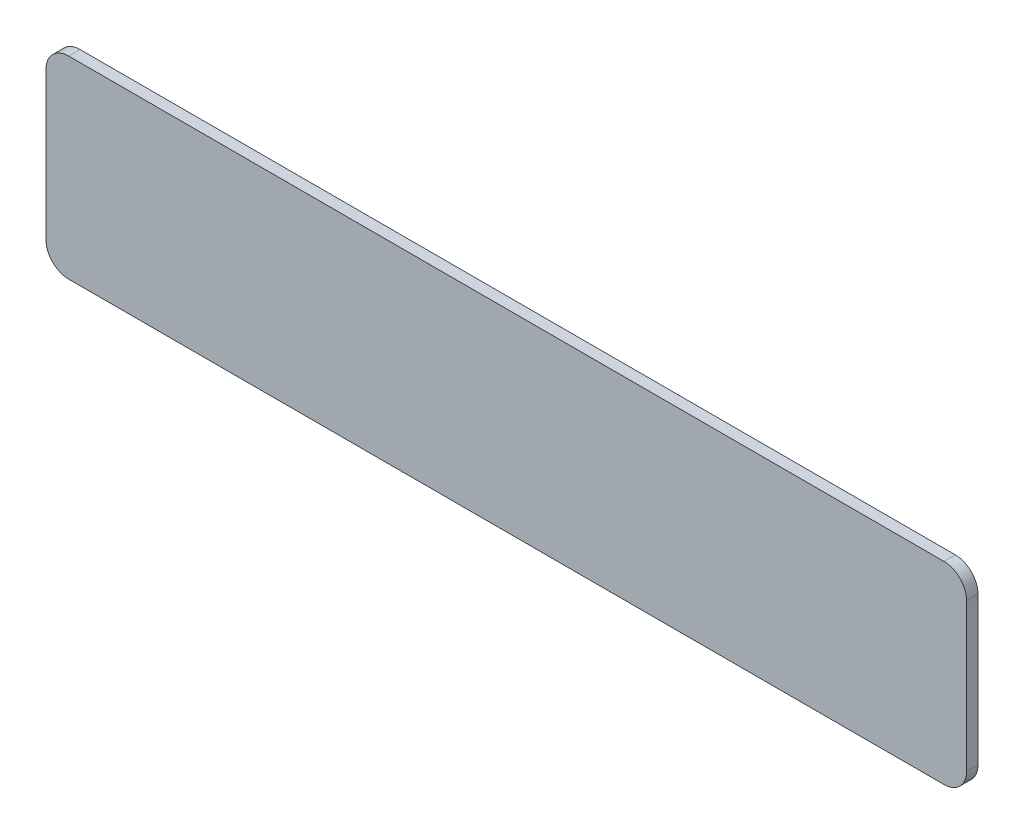
SolidWorks part; units mm, degrees
ref_plane "Front Plane" through (0, 0, 0) normal (0, 0, 1) x (1, 0, 0)
ref_plane "Top Plane" through (0, 0, 0) normal (0, 1, 0) x (1, 0, 0)
ref_plane "Right Plane" through (0, 0, 0) normal (1, 0, 0) x (0, 0, -1)
sketch "Sketch1" plane through (0, 0, 0) normal (0, 0, 1) x (1, 0, 0)
  line L1 (-38.5, 8.5) -> (38.5, 8.5)
  line L2 (-40.5, 6.5) -> (-40.5, -6.5)
  line L3 (-38.5, -8.5) -> (38.5, -8.5)
  line L4 (40.5, 6.5) -> (40.5, -6.5)
  line L5 (-40.5, 8.5) -> (40.5, -8.5) construction
  line L6 (-40.5, -8.5) -> (40.5, 8.5) construction
  arc A0 (38.5, 8.5) -> (40.5, 6.5) centre (38.5, 6.5) cw
  arc A1 (38.5, -8.5) -> (40.5, -6.5) centre (38.5, -6.5) ccw
  arc A2 (-40.5, -6.5) -> (-38.5, -8.5) centre (-38.5, -6.5) ccw
  arc A3 (-38.5, 8.5) -> (-40.5, 6.5) centre (-38.5, 6.5) ccw
  point P0 (0, 0)
  dimension "D3" = 2
  dimension "D1" = 81
  dimension "D2" = 17
extrude "Boss-Extrude1" add sketch "Sketch1" along normal blind 1
